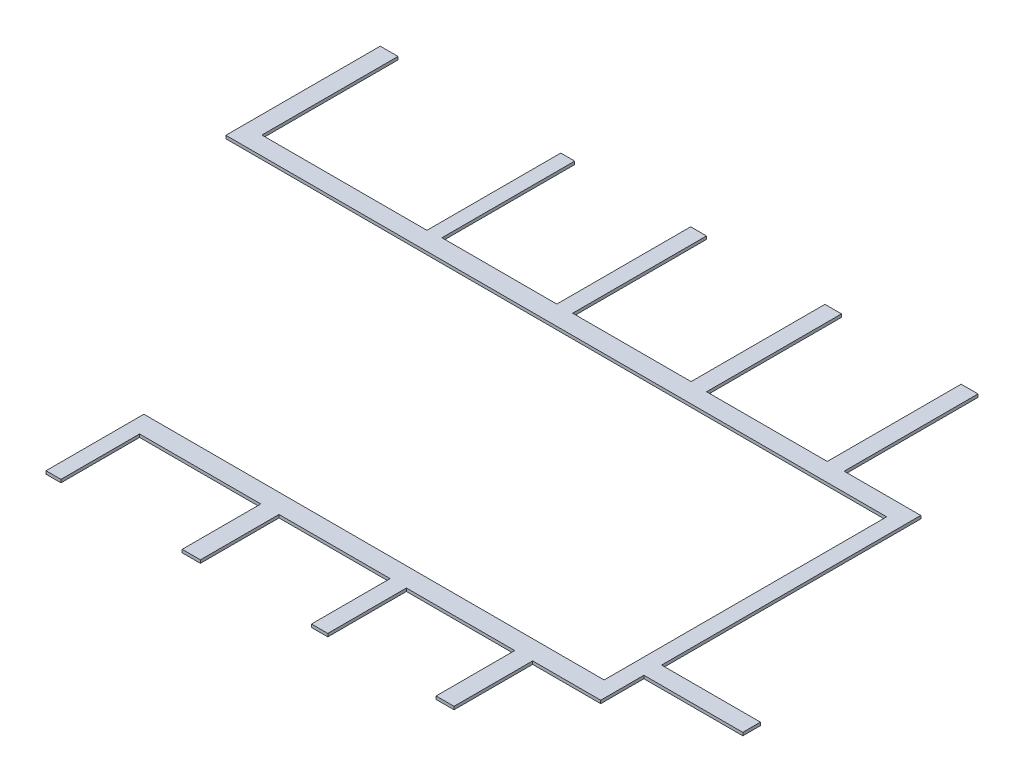
SolidWorks part; units mm, degrees
ref_plane "Alzado" through (0, 0, 0) normal (0, 0, 1) x (1, 0, 0)
ref_plane "Planta" through (0, 0, 0) normal (0, 1, 0) x (1, 0, 0)
ref_plane "Vista lateral" through (0, 0, 0) normal (1, 0, 0) x (0, 0, -1)
sketch "Croquis1" plane through (0, 0, 0) normal (0, 1, 0) x (1, 0, 0)
  line L0 (-4448.6782, -7294) -> (-4448.6782, -8309)
  line L2 (-4448.6782, -8309) -> (-503.725, -8309)
  line L3 (-503.725, -8189) -> (-503.725, -7309)
  line L5 (-503.725, -7309) -> (-614.5949, -7309)
  line L6 (-614.5949, -7309) -> (-614.5949, -8189)
  line L7 (-614.5949, -8189) -> (-1408.2166, -8189)
  line L8 (-1408.2166, -8189) -> (-1408.2166, -7302)
  line L10 (-1408.2166, -7302) -> (-1516.9685, -7302)
  line L11 (-1516.9685, -7302) -> (-1516.9685, -8182)
  line L12 (-1516.9685, -8182) -> (-2295.6855, -8182)
  line L13 (-2295.6855, -8182) -> (-2295.6855, -7302)
  line L15 (-2295.6855, -7302) -> (-2399.8238, -7302)
  line L16 (-2399.8238, -7302) -> (-2399.8238, -8182)
  line L17 (-2399.8238, -8182) -> (-3154.9887, -8182)
  line L18 (-3154.9887, -8182) -> (-3154.9887, -7309)
  line L20 (-3154.9887, -7309) -> (-3246.7298, -7309)
  line L21 (-3246.7298, -7309) -> (-3246.7298, -8189)
  line L22 (-3246.7298, -8189) -> (-4331.8053, -8189)
  line L23 (-4331.8053, -8189) -> (-4331.8053, -7294)
  line L24 (-4331.8053, -7294) -> (-4448.6782, -7294)
  line L25 (-503.725, -8309) -> (-104.0965, -8309)
  line L26 (-104.0965, -8309) -> (-104.0965, -10009)
  line L27 (0, -10009) -> (650, -10009)
  line L29 (650, -10009) -> (650, -9892.9604)
  line L30 (650, -9892.9604) -> (0, -9892.9604)
  line L31 (0, -9892.9604) -> (0, -8189)
  line L32 (0, -8189) -> (-503.725, -8189)
  line L33 (0, -10009) -> (0, -10293.0436)
  line L34 (0, -10293.0436) -> (-447.5228, -10293.0436)
  line L35 (-3031.774, -10293.0436) -> (-3031.774, -10810)
  line L37 (-104.0965, -10009) -> (-104.0965, -10166.5398)
  line L38 (-104.0965, -10166.5398) -> (-3130.1253, -10166.5398)
  line L39 (-3130.1253, -10166.5398) -> (-3130.1253, -10810)
  line L40 (-3130.1253, -10810) -> (-3031.774, -10810)
  line L41 (-2115.1692, -10293.0436) -> (-2115.1692, -10810)
  line L43 (-2115.1692, -10810) -> (-2234.9032, -10810)
  line L44 (-2234.9032, -10810) -> (-2234.9032, -10293.0436)
  line L45 (-2234.9032, -10293.0436) -> (-3031.774, -10293.0436)
  line L46 (-1277.5468, -10293.0436) -> (-1277.5468, -10810)
  line L48 (-1277.5468, -10810) -> (-1384.6596, -10810)
  line L49 (-1384.6596, -10810) -> (-1384.6596, -10293.0436)
  line L50 (-1384.6596, -10293.0436) -> (-2115.1692, -10293.0436)
  line L51 (-447.5228, -10293.0436) -> (-447.5228, -10810)
  line L53 (-447.5228, -10810) -> (-565.3603, -10810)
  line L54 (-565.3603, -10810) -> (-565.3603, -10293.0436)
  line L55 (-565.3603, -10293.0436) -> (-1277.5468, -10293.0436)
  dimension "D1" = 1000
  dimension "D2" = 880
  dimension "D3" = 880
  dimension "D4" = 880
  dimension "D5" = 880
  dimension "D6" = 1700
  dimension "D7" = 650
extrude "Saliente-Extruir1" add sketch "Croquis1" along normal blind 20
